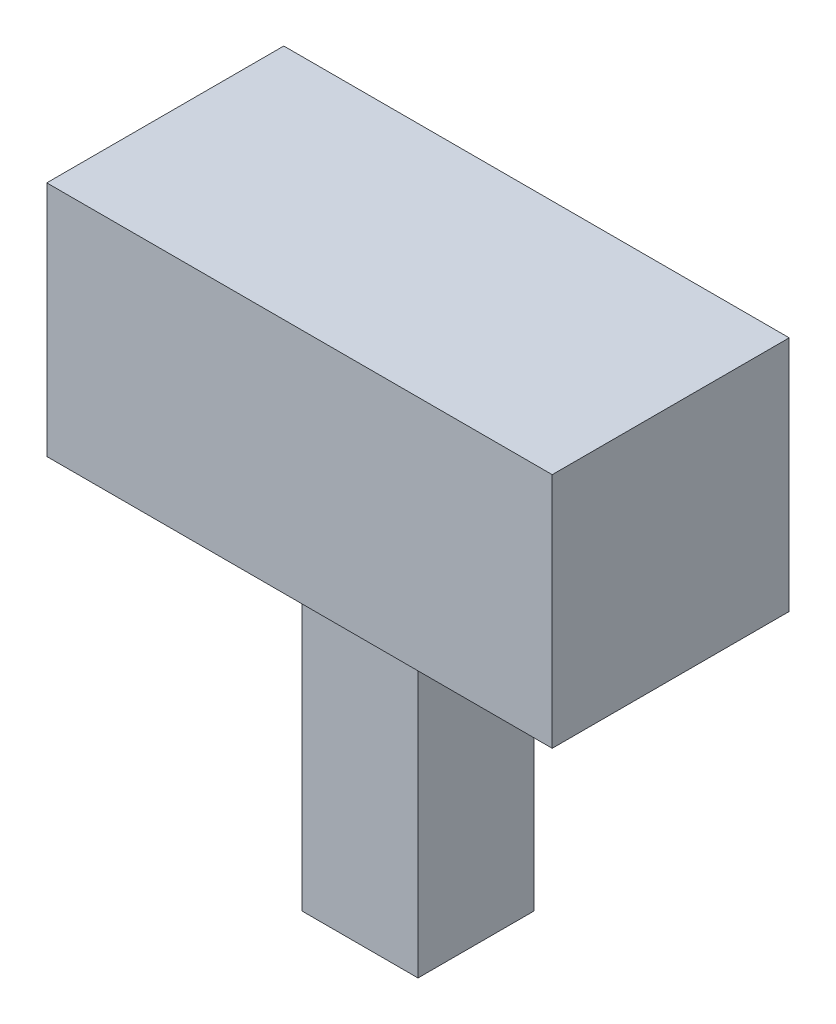
SolidWorks part; units mm, degrees
ref_plane "前视基准面" through (0, 0, 0) normal (0, 0, 1) x (1, 0, 0)
ref_plane "上视基准面" through (0, 0, 0) normal (0, 1, 0) x (1, 0, 0)
ref_plane "右视基准面" through (0, 0, 0) normal (1, 0, 0) x (0, 0, -1)
other "Configuration Table"
sketch "草图1" plane through (0, 0, 0) normal (0, 0, 1) x (1, 0, 0)
  line L1 (-4.1436, 5.1631) -> (5.6564, 5.1631)
  line L2 (-4.1436, 5.1631) -> (-4.1436, -4.6369)
  line L3 (-4.1436, -4.6369) -> (5.6564, -4.6369)
  line L4 (5.6564, 5.1631) -> (5.6564, -4.6369)
  dimension "D1" = 9.8
  dimension "D2" = 9.8
extrude "凸台-拉伸1" add sketch "草图1" along normal blind 9.8
sketch "草图2" plane through (0, -4.6369, 0) normal (0, -1, 0) x (1, 0, 0)
  line L0 (-4.1436, 9.8) -> (5.6564, 0) construction
  line L1 (5.6564, 9.8) -> (-4.1436, 0) construction
  line L3 (-1.6436, 2.5) -> (3.1564, 2.5)
  line L4 (-1.6436, 2.5) -> (-1.6436, 7.3)
  line L5 (-1.6436, 7.3) -> (3.1564, 7.3)
  line L6 (3.1564, 2.5) -> (3.1564, 7.3)
  line L7 (0.7564, 7.3) -> (0.7564, 2.5) construction
  line L8 (-1.6436, 4.9) -> (3.1564, 4.9) construction
  point P8 (0.7564, 4.9)
  dimension "D1" = 4.8
extrude "凸台-拉伸2" add sketch "草图2" along normal blind 13.5
sketch "草图4" plane through (5.6564, 0, 0) normal (1, 0, 0) x (0, 0, -1)
  line L1 (-9.8, 5.1631) -> (0, 5.1631)
  line L2 (-9.8, 5.1631) -> (-9.8, -4.6369)
  line L3 (-9.8, -4.6369) -> (0, -4.6369)
  line L4 (0, 5.1631) -> (0, -4.6369)
extrude "凸台-拉伸4" add sketch "草图4" along normal blind 5.55
sketch "草图6" plane through (-4.1436, 0, 0) normal (-1, 0, 0) x (0, 0, 1)
  line L14 (0, 5.1631) -> (0, -4.6369)
  line L15 (0, -4.6369) -> (9.8, -4.6369)
  line L16 (9.8, -4.6369) -> (9.8, 5.1631)
  line L17 (9.8, 5.1631) -> (0, 5.1631)
  line L18 (0, 5.1631) -> (0, -4.6369)
  line L19 (0, -4.6369) -> (9.8, -4.6369)
  line L20 (9.8, -4.6369) -> (9.8, 5.1631)
  line L21 (9.8, 5.1631) -> (0, 5.1631)
  dimension "D1" = 0
extrude "凸台-拉伸5" add sketch "草图6" along normal blind 5.55 and the other way up to surface (15.35 mm away) other way up to face at (11.2064, 0.2631, 4.9)
sketch "草图7" plane through (0, 0, 0) normal (0, 0, -1) x (-1, 0, 0)
  text T0 "98\r\n"
extrude "切除-拉伸1" cut sketch "草图7" against normal blind 1
sketch "草图8" plane through (0, 0, 0) normal (0, 0, -1) x (-1, 0, 0)
  text T0 "48\r\n"
extrude "切除-拉伸2" cut sketch "草图8" against normal blind 1
